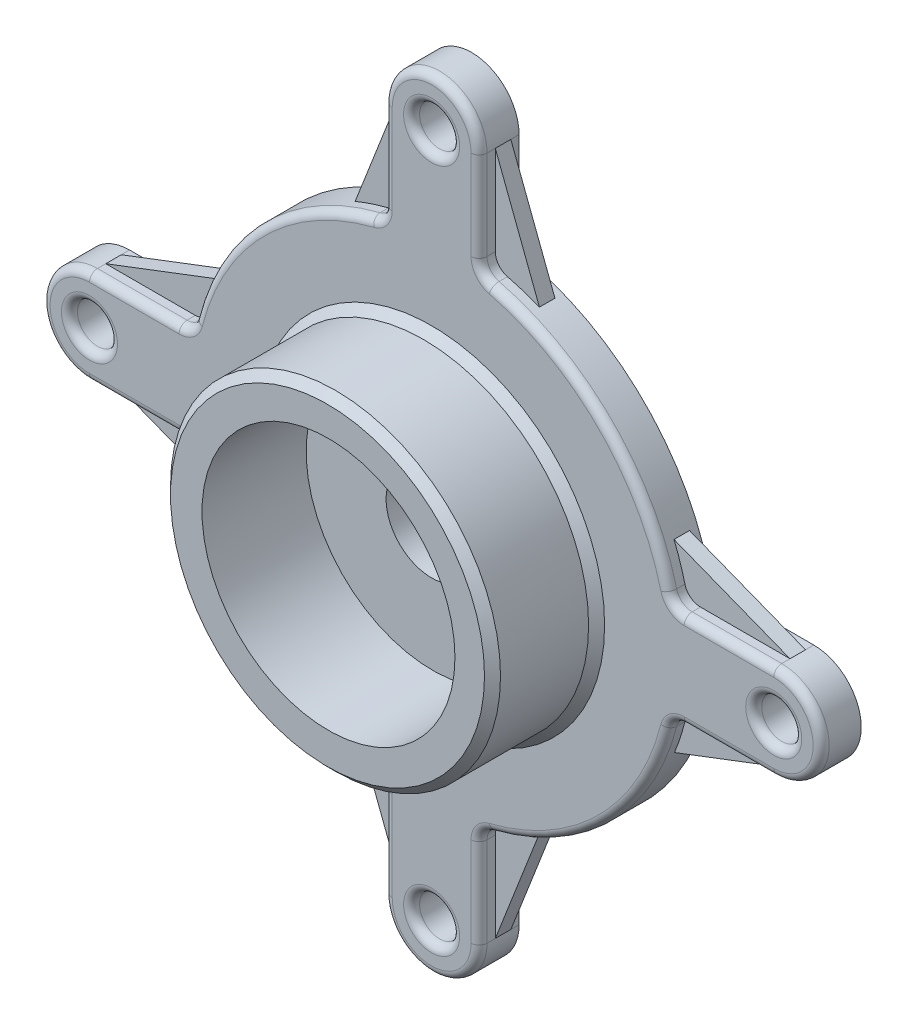
SolidWorks part; units mm, degrees
ref_plane "Front Plane" through (0, 0, 0) normal (0, 0, 1) x (1, 0, 0)
ref_plane "Top Plane" through (0, 0, 0) normal (0, 1, 0) x (1, 0, 0)
ref_plane "Right Plane" through (0, 0, 0) normal (1, 0, 0) x (0, 0, -1)
sketch "Sketch1" plane through (0, 0, 0) normal (0, 0, 1) x (1, 0, 0)
  line L0 (-108.4993, 15.042) -> (-80.1026, 15.042)
  line L1 (-108.4993, -15.042) -> (-80.1026, -15.042)
  line L2 (15.042, 108.4993) -> (15.042, 80.1026)
  line L3 (-15.042, 108.4993) -> (-15.042, 80.1026)
  line L4 (108.4993, -15.042) -> (80.1026, -15.042)
  line L5 (108.4993, 15.042) -> (80.1026, 15.042)
  line L6 (-15.042, -108.4993) -> (-15.042, -80.1026)
  line L7 (15.042, -108.4993) -> (15.042, -80.1026)
  arc A0 (-18.8843, 75.1757) -> (-75.1757, 18.8843) centre (0, 0) ccw
  circle A1 centre (-108.4993, 0) radius 6.35
  arc A2 (15.042, 108.4993) -> (-15.042, 108.4993) centre (0, 108.4993) ccw
  circle A3 centre (0, 108.4993) radius 6.35
  arc A4 (108.4993, -15.042) -> (108.4993, 15.042) centre (108.4993, 0) ccw
  arc A5 (-108.4993, 15.042) -> (-108.4993, -15.042) centre (-108.4993, 0) ccw
  circle A6 centre (108.4993, 0) radius 6.35
  arc A7 (-15.042, -108.4993) -> (15.042, -108.4993) centre (0, -108.4993) ccw
  circle A8 centre (0, -108.4993) radius 6.35
  arc A9 (-75.1757, -18.8843) -> (-18.8843, -75.1757) centre (0, 0) ccw
  arc A10 (18.8843, -75.1757) -> (75.1757, -18.8843) centre (0, 0) ccw
  arc A11 (75.1757, 18.8843) -> (18.8843, 75.1757) centre (0, 0) ccw
  arc A12 (-15.042, 80.1026) -> (-18.8843, 75.1757) centre (-20.122, 80.1026) cw
  arc A13 (15.042, 80.1026) -> (18.8843, 75.1757) centre (20.122, 80.1026) ccw
  arc A14 (80.1026, 15.042) -> (75.1757, 18.8843) centre (80.1026, 20.122) cw
  arc A15 (80.1026, -15.042) -> (75.1757, -18.8843) centre (80.1026, -20.122) ccw
  arc A16 (15.042, -80.1026) -> (18.8843, -75.1757) centre (20.122, -80.1026) cw
  arc A17 (-15.042, -80.1026) -> (-18.8843, -75.1757) centre (-20.122, -80.1026) ccw
  arc A18 (-80.1026, -15.042) -> (-75.1757, -18.8843) centre (-80.1026, -20.122) cw
  arc A19 (-80.1026, 15.042) -> (-75.1757, 18.8843) centre (-80.1026, 20.122) ccw
  point P39 (-76.0377, -15.042)
  dimension "D1" = 12.7
  dimension "D3" = 5.08
  dimension "D2" = 30.988
extrude "Extrude1" add sketch "Sketch1" along normal blind 12.7
sketch "Sketch3" plane through (-17.1394, 18.8771, 12.7) normal (0, 0, 1) x (1, 0, 0)
  circle A0 centre (17.1394, -18.8771) radius 52.3279
  circle A1 centre (17.4547, -18.4245) radius 40.1114
  dimension "D1" = 104.6558
extrude "Extrude3" add sketch "Sketch3" along normal blind 33.02
chamfer "Chamfer1" distance 2.54 angle 45 1 edges at (52.3279, 0, 45.72)
chamfer "Chamfer2" distance 2.54 angle 45 1 edges at (-52.3279, 0, 12.7)
sketch "Sketch6" plane through (-20.5652, 19.9273, 0) normal (0, 0, -1) x (-1, 0, 0)
  circle A0 centre (-20.5652, -19.9273) radius 52.3279
  dimension "D1" = 104.6558
extrude "Extrude4" add sketch "Sketch6" along normal blind 17.78
sketch "Sketch7" plane through (-3.0784, -13.3875, -17.78) normal (0, 0, -1) x (-1, 0, 0)
  circle A0 centre (-3.0784, 13.3875) radius 35.56
  dimension "D1" = 71.12
extrude "Cut-Extrude2" cut sketch "Sketch7" against normal blind 10.16
sketch "Sketch5" plane through (3.3166, -11.2868, 12.7) normal (0, 0, 1) x (1, 0, 0)
  circle A0 centre (-3.3166, 11.2868) radius 14.4337
extrude "Cut-Extrude1" cut sketch "Sketch5" against normal through all
chamfer "Chamfer3" distance 2.54 angle 45 3 edges at (-52.3279, 0, 0) (-35.56, 0, -17.78) (-52.3279, 0, -17.78)
fillet "Fillet1" radius 2.54 28 edges at (-15.042, 94.3009, 12.7) (0, 123.5412, 12.7) (15.042, 94.3009, 12.7) (16.1161, 76.9786, 12.7) (54.8087, 54.8087, 12.7) (76.9786, 16.1161, 12.7) (94.3009, 15.042, 12.7) (123.5412, 0, 12.7) (94.3009, -15.042, 12.7) (76.9786, -16.1161, 12.7) (54.8087, -54.8087, 12.7) (16.1161, -76.9786, 12.7) (15.042, -94.3009, 12.7) (0, -123.5412, 12.7) (-15.042, -94.3009, 12.7) (-16.1161, -76.9786, 12.7) (-54.8087, -54.8087, 12.7) (-76.9786, -16.1161, 12.7) (-94.3009, -15.042, 12.7) (-123.5412, 0, 12.7) (-94.3009, 15.042, 12.7) (-76.9786, 16.1161, 12.7) (-54.8087, 54.8087, 12.7) (-16.1161, 76.9786, 12.7) (6.35, 108.4993, 12.7) (114.8493, 0, 12.7) (6.35, -108.4993, 12.7) (-102.1493, 0, 12.7)
ref_plane "Plane1" through (0, 0, 5.08) normal (0, 0, 1) x (1, 0, 0)
sketch "Sketch8" plane through (0, 0, 5.08) normal (0, 0, 1) x (1, 0, 0)
  line L0 (-15.042, 108.4993) -> (-29.4095, 71.7152)
  arc A0 (-18.8843, 75.1757) -> (-75.1757, 18.8843) centre (0, 0) ccw construction
rib "Rib1" sketch "Sketch8" sketch "Sketch8" thickness 4.92 extrusion direction parallel to sketch draft on no parameters "D1"=4.92
pattern_circular "CirPattern1" count 4 over 360 about axis through (0, 0, 0) along (0, 0, 1) of "Rib1"
sketch "Sketch9" plane through (0, 0, 5.08) normal (0, 0, 1) x (1, 0, 0)
  line L0 (15.042, 108.4993) -> (29.0303, 71.8696)
  arc A0 (75.1757, 18.8843) -> (18.8843, 75.1757) centre (0, 0) ccw construction
rib "Rib2" sketch "Sketch9" sketch "Sketch9" thickness 4.92 extrusion direction parallel to sketch draft on no parameters "D1"=4.92
pattern_circular "CirPattern2" count 4 over 360 about axis through (0, 0, 0) along (0, 0, 1) of "Rib2"
